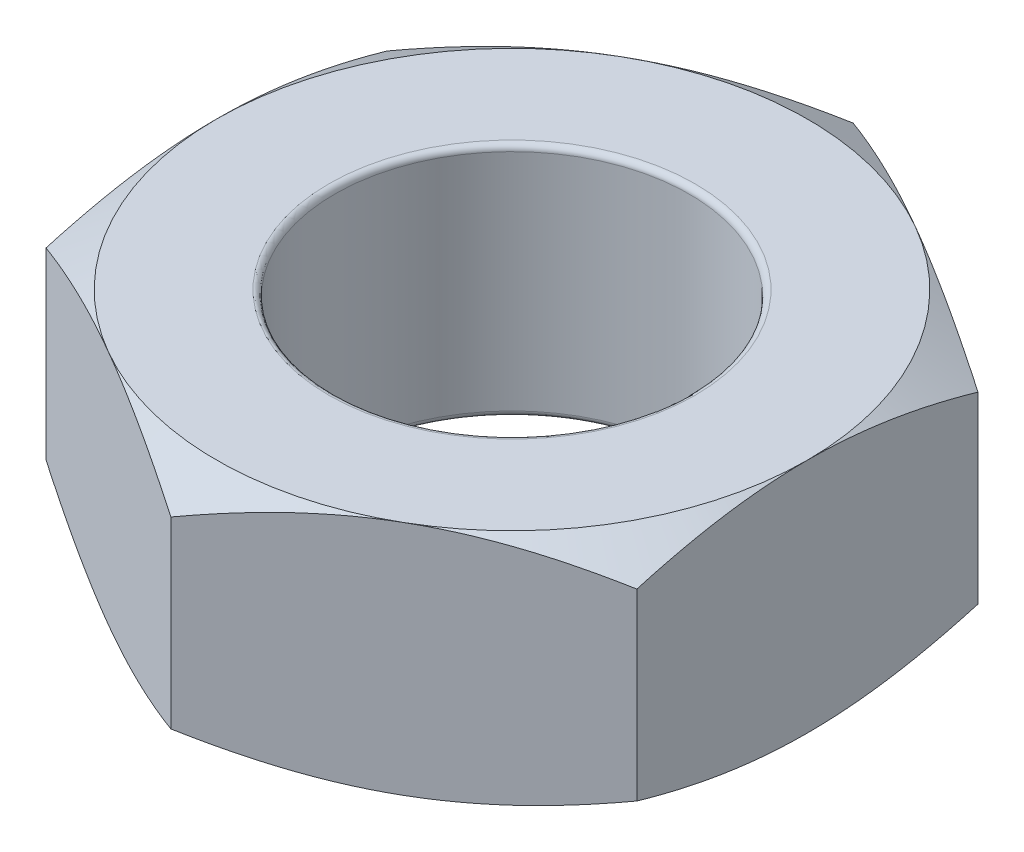
SolidWorks part; units mm, degrees
ref_plane "Front Plane" through (0, 0, 0) normal (0, 0, 1) x (1, 0, 0)
ref_plane "Top Plane" through (0, 0, 0) normal (0, 1, 0) x (1, 0, 0)
ref_plane "Right Plane" through (0, 0, 0) normal (1, 0, 0) x (0, 0, -1)
sketch "Sketch2" plane through (0, 0, 0) normal (0, 1, 0) x (1, 0, 0)
  line L1 (2.5, -1.4434) -> (2.5, 1.4434)
  line L2 (2.5, 1.4434) -> (0, 2.8868)
  line L3 (0, 2.8868) -> (-2.5, 1.4434)
  line L4 (-2.5, 1.4434) -> (-2.5, -1.4434)
  line L5 (-2.5, -1.4434) -> (0, -2.8868)
  line L6 (0, -2.8868) -> (2.5, -1.4434)
  circle A0 centre (0, 0) radius 1.5
  circle A1 centre (0, 0) radius 2.5 construction
  point P3 (0, 0)
  dimension "D1" = 3
  dimension "D2" = 5
extrude "Boss-Extrude1" add sketch "Sketch2" along normal blind 2
sketch "Sketch3" plane through (0, 2, 0) normal (0, 1, 0) x (1, 0, 0)
  circle A0 centre (0, 0) radius 2.5 construction
  circle A1 centre (0, 0) radius 2.5
extrude "Cut-Extrude1" cut sketch "Sketch3" against normal blind 2 draft 60 flip side to cut
sketch "Sketch4" plane through (0, 0, 0) normal (0, -1, 0) x (1, 0, 0)
  circle A0 centre (0, 0) radius 2.5 construction
  circle A1 centre (0, 0) radius 2.5
extrude "Cut-Extrude2" cut sketch "Sketch4" against normal blind 2 draft 60 flip side to cut
fillet "Fillet1" radius 0.05 2 edges at (0, 0, 1.5) (0, 2, 1.5)
